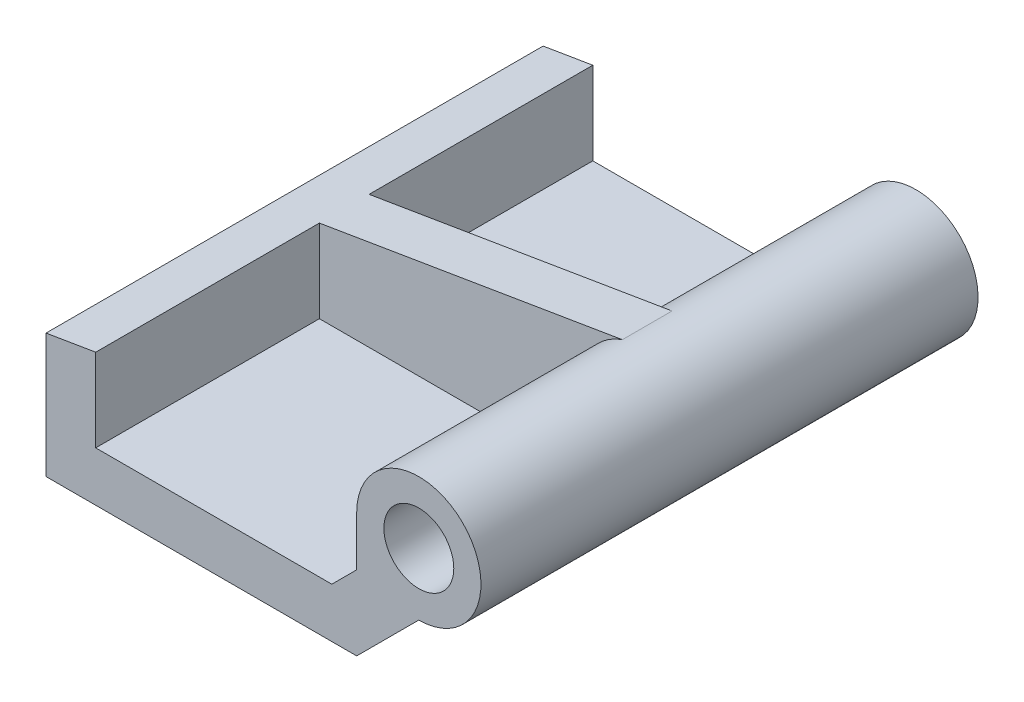
SolidWorks part; units mm, degrees
ref_plane "Front Plane" through (0, 0, 0) normal (0, 0, 1) x (1, 0, 0)
ref_plane "Top Plane" through (0, 0, 0) normal (0, 1, 0) x (1, 0, 0)
ref_plane "Right Plane" through (0, 0, 0) normal (1, 0, 0) x (0, 0, -1)
sketch "Sketch1" plane through (0, 0, 0) normal (0, 0, 1) x (1, 0, 0)
  line L0 (5.338, 21.2912) -> (24.388, 24.4662)
  line L1 (5.338, 14.9412) -> (24.388, 14.9412)
  line L2 (5.338, 14.9412) -> (5.338, 21.2912)
  line L3 (5.338, 21.2912) -> (24.388, 21.2912)
  line L4 (24.388, 14.9412) -> (24.388, 21.2912)
  line L5 (24.388, 24.4662) -> (24.388, 21.2912)
  dimension "D1" = 19.05
  dimension "D2" = 6.35
  dimension "D3" = 3.175
extrude "Boss-Extrude1" add sketch "Sketch1" against normal blind 25.4 contours L5 L0 L3 | L1 L4 L3 L2
sketch "Sketch2" plane through (0, 0, 0) normal (0, 0, 1) x (1, 0, 0)
  line L0 (24.388, 24.4662) -> (24.388, 14.9412) construction
  circle A0 centre (24.388, 21.2912) radius 3.175
  arc A1 (22.1429, 19.0461) -> (23.3582, 24.2946) centre (24.388, 21.2912) cw
  point P4 (0, 0)
  point P13 (0, 0)
  dimension "D1" = 6.35
  dimension "D2" = 3.175
extrude "Boss-Extrude3" add sketch "Sketch2" against normal up to surface (25.4 mm away) contours A0 up to face at (14.863, 18.9099, -25.4)
sketch "Sketch9" plane through (0, 0, 0) normal (0, 0, 1) x (1, 0, 0)
  line L0 (23.3582, 24.2946) -> (7.878, 21.7145)
  line L1 (5.338, 21.2912) -> (23.3582, 24.2946) construction
  line L2 (5.338, 14.9412) -> (24.388, 14.9412) construction
  line L3 (7.878, 21.7145) -> (7.878, 17.4812)
  line L4 (7.878, 17.4812) -> (19.943, 17.4812)
  line L5 (19.943, 17.4812) -> (21.213, 18.7512)
  line L6 (21.213, 18.7512) -> (21.213, 21.2912)
  arc A0 (23.3582, 24.2946) -> (21.213, 21.2912) centre (24.388, 21.2912) ccw
  point P5 (7.878, 21.2912)
  point P9 (7.878, 17.4812)
  dimension "D1" = 2.54
  dimension "D2" = 0
  dimension "D3" = 2.54
  dimension "D4" = 1.27
  dimension "D5" = 0
  dimension "D6" = 1.27
extrude "Cut-Extrude5" cut sketch "Sketch9" against normal blind 11.43
sketch "Sketch10" plane through (0, 0, 0) normal (0, 0, 1) x (1, 0, 0)
  line L0 (24.388, 18.1162) -> (21.213, 14.9412)
  line L1 (5.338, 14.9412) -> (24.388, 14.9412) construction
  line L2 (21.213, 14.9412) -> (24.388, 14.9412)
  line L3 (24.388, 14.9412) -> (24.388, 18.1162)
extrude "Cut-Extrude6" cut sketch "Sketch10" against normal through all contours L0 L2 L3
sketch "Sketch17" plane through (0, 0, -25.4) normal (0, 0, -1) x (-1, 0, 0)
  line L0 (-23.3582, 24.2946) -> (-7.878, 21.7145)
  line L1 (-7.878, 21.7145) -> (-7.878, 17.4812)
  line L2 (-7.878, 17.4812) -> (-19.943, 17.4812)
  line L3 (-19.943, 17.4812) -> (-21.213, 18.7512)
  line L4 (-21.213, 18.7512) -> (-21.213, 21.2912)
  line L5 (-21.213, 21.2912) -> (-21.213, 18.7512)
  arc A0 (-21.213, 21.2912) -> (-23.3582, 24.2946) centre (-24.388, 21.2912) ccw
  line M5 (-5.338, 21.2912) -> (-23.3582, 24.2946)
extrude "Cut-Extrude9" cut sketch "Sketch17" against normal blind 11.43 contours A0 L4 L3 L2 L1 M5
hole_wizard "9/64 (0.14063) Diameter Hole3" positions "3DSketch3" profile "Sketch18" hole size "9/64" standard "ANSI Inch" end condition through all
sketch3d "3DSketch3"
  point P0 (24.388, 21.2912, 0)
sketch "Sketch18" plane through (24.388, 21.2912, 0) normal (1, 0, 0) x (0, -1, 0)
  line L0 (0, 0) -> (0, 25.4)
  line L1 (0, 25.4) -> (1.786, 25.4)
  line L2 (1.786, 25.4) -> (1.786, 0)
  line L5 (1.786, 0) -> (0, 0)
  line L11 (0, -6.35) -> (0, 107.95) construction
  dimension "Thru Hole Dia." = 3.572
  dimension "Thru Hole Depth" = 25.4
